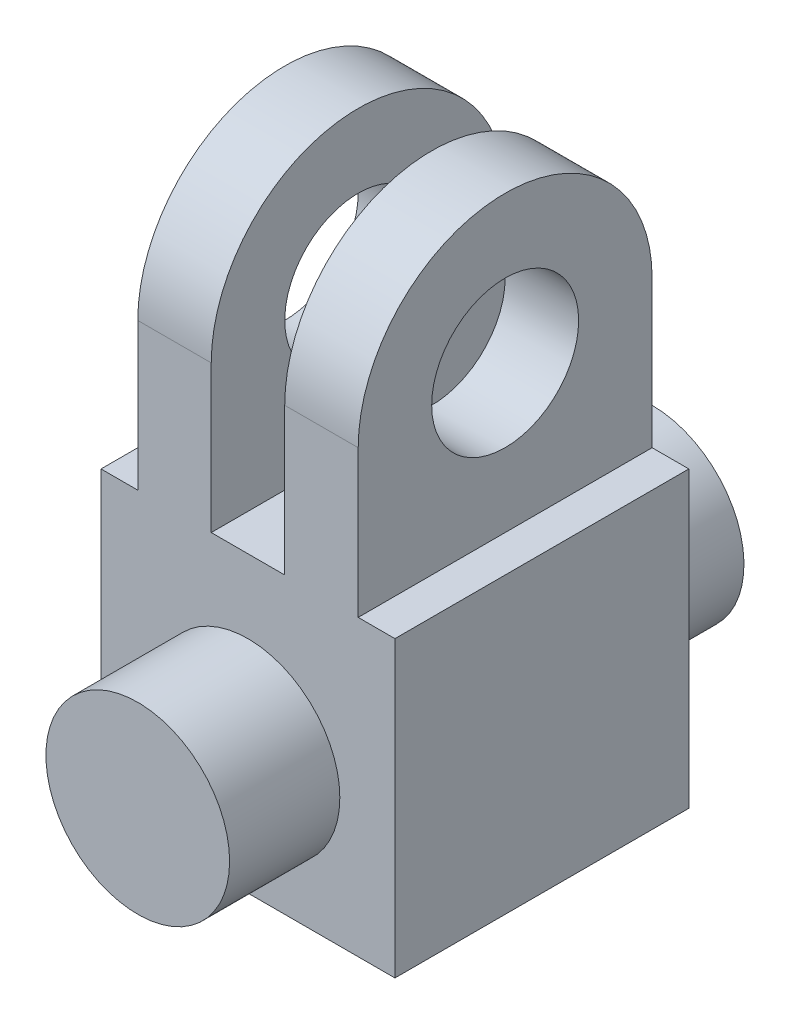
SolidWorks part; units mm, degrees
ref_plane "Alzado" through (0, 0, 0) normal (0, 0, 1) x (1, 0, 0)
ref_plane "Planta" through (0, 0, 0) normal (0, 1, 0) x (1, 0, 0)
ref_plane "Vista lateral" through (0, 0, 0) normal (1, 0, 0) x (0, 0, -1)
sketch "Croquis2" plane through (0, 0, 0) normal (1, 0, 0) x (0, 0, -1)
  line L0 (0, 0) -> (80, 0)
  line L1 (80, 0) -> (80, 120)
  line L2 (0, 120) -> (0, 0)
  arc A0 (80, 120) -> (0, 120) centre (40, 120) ccw
  circle A1 centre (40, 120) radius 20
  dimension "D3" = 40
  dimension "D1" = 80
  dimension "D2" = 120
extrude "Saliente-Extruir1" add sketch "Croquis2" against normal blind 80
sketch "Croquis3" plane through (0, 0, 0) normal (0, 0, 1) x (1, 0, 0)
  line L0 (0, 120) -> (0, 0) construction
  line L1 (0, 80) -> (-10, 80)
  line L2 (-10, 80) -> (-10, 160)
  line L3 (0, 160) -> (-80, 160) construction
  line L4 (-10, 160) -> (0, 160)
  line L5 (0, 160) -> (0, 80)
  line L6 (-80, 80) -> (-70, 80)
  line L7 (-80, 120) -> (-80, 0) construction
  line L8 (-70, 80) -> (-70, 160)
  line L9 (-70, 160) -> (-80, 160)
  line L10 (-80, 160) -> (-80, 80)
  line L11 (-50, 80) -> (-30, 80)
  line L12 (-30, 80) -> (-30, 160)
  line L13 (-30, 160) -> (-50, 160)
  line L14 (-50, 160) -> (-50, 80)
  line L15 (-80, 0) -> (0, 0) construction
  point P18 (-49.504, 95.14)
  dimension "D1" = 80
  dimension "D2" = 10
  dimension "D3" = 20
  dimension "D4" = 20
extrude "Cortar-Extruir1" cut sketch "Croquis3" against normal up to next
sketch "Croquis4" plane through (0, 0, 0) normal (0, 0, 1) x (1, 0, 0)
  line L0 (-80, 0) -> (0, 0) construction
  line L2 (0, 80) -> (0, 0) construction
  circle A0 centre (-40, 35) radius 25
  point P6 (0, 20.2134)
  dimension "D3" = 50
  dimension "D1" = 35
  dimension "D2" = 40
extrude "Saliente-Extruir2" add sketch "Croquis4" along normal blind 30
sketch "Croquis5" plane through (0, 0, -80) normal (0, 0, -1) x (-1, 0, 0)
  circle A0 centre (40, 35) radius 25 construction
  circle A1 centre (40, 35) radius 25
extrude "Saliente-Extruir3" add sketch "Croquis5" along normal blind 30
